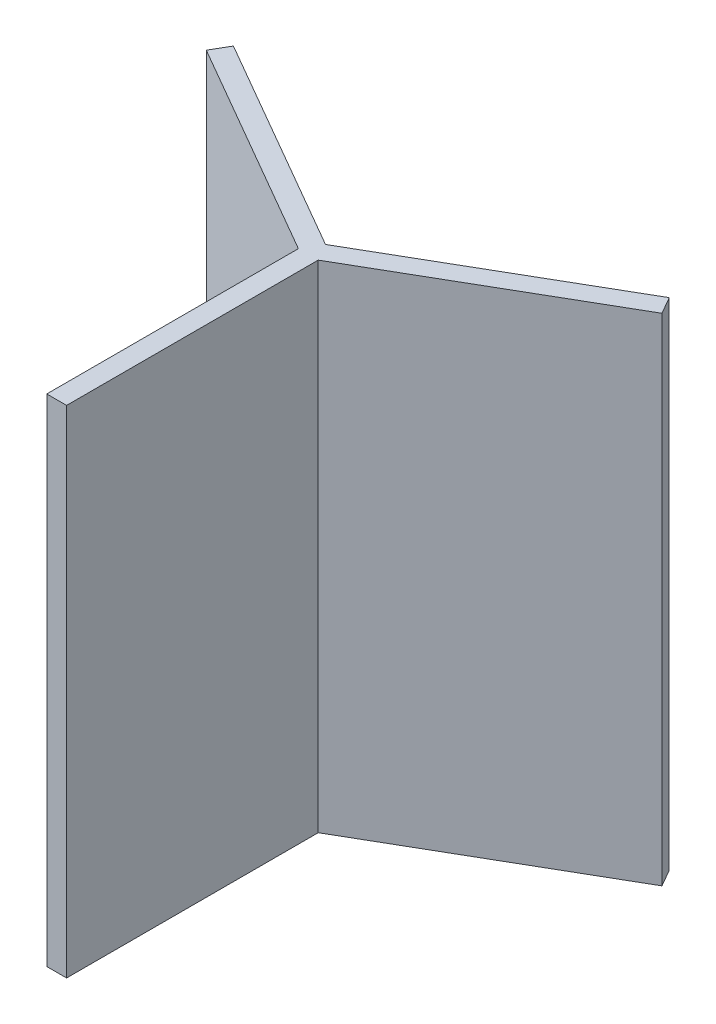
SolidWorks part; units mm, degrees
ref_plane "Front Plane" through (0, 0, 0) normal (0, 0, 1) x (1, 0, 0)
ref_plane "Top Plane" through (0, 0, 0) normal (0, 1, 0) x (1, 0, 0)
ref_plane "Right Plane" through (0, 0, 0) normal (1, 0, 0) x (0, 0, -1)
sketch "Sketch1" plane through (0, 0, 0) normal (0, 1, 0) x (1, 0, 0)
  line L0 (0, 0) -> (-2247.23, 1297.4389) construction
  line L1 (-100, -2594.8777) -> (100, -2594.8777)
  line L4 (0, 0) -> (0, -2594.8777) construction
  line L5 (-100, -2594.8777) -> (-100, -57.735)
  line L6 (0, 0) -> (100, 0) construction
  line L7 (100, -2594.8777) -> (100, -57.735)
  line L8 (-100, -2594.8777) -> (100, 0) construction
  line L9 (-100, 0) -> (100, -2594.8777) construction
  line L10 (-2297.23, 1210.8363) -> (-100, -57.735)
  line L11 (-2197.23, 1384.0414) -> (0, 115.4701)
  line L12 (-2197.23, 1384.0414) -> (-2297.23, 1210.8363)
  line L13 (50, 86.6025) -> (0, 0) construction
  line L14 (0, 0) -> (2247.23, 1297.4389) construction
  line L15 (2197.23, 1384.0414) -> (0, 115.4701)
  line L16 (2297.23, 1210.8363) -> (100, -57.735)
  line L17 (2297.23, 1210.8363) -> (2197.23, 1384.0414)
  line L18 (50, -86.6025) -> (0, 0) construction
  line L19 (0, 0) -> (-50, -86.6025) construction
  line L20 (-95.3428, -60.4238) -> (-50, -86.6025) construction
  line L21 (-100, 0) -> (0, 0) construction
  line L22 (0, 0) -> (-50, 86.6025) construction
  line L23 (100, -57.735) -> (100, 0) construction
  line L24 (-100, -57.735) -> (-100, 0) construction
  line L25 (0, 115.4701) -> (-50, 86.6025) construction
  line L26 (0, 115.4701) -> (50, 86.6025) construction
  line L27 (95.3428, -60.4238) -> (50, -86.6025) construction
  line L28 (100, -57.735) -> (95.3428, -60.4238) construction
  line L29 (-100, -57.735) -> (-95.3428, -60.4238) construction
  arc A0 (0, -2594.8777) -> (2124.6635, 1489.6964) centre (0, 0) ccw construction
  arc A1 (2124.6635, 1489.6964) -> (-2046.724, 1595.0897) centre (0, 0) ccw construction
  arc A2 (-2046.724, 1595.0897) -> (0, -2594.8777) centre (0, 0) ccw construction
  point P1 (-1023.362, 797.5449)
  point P3 (1062.3318, 744.8482)
  point P4 (0, -1297.4389)
  point P5 (0, -1297.4389)
  point P8 (0, 0)
  dimension "D1" = 200
  dimension "D2" = 3
extrude "Boss-Extrude1" add sketch "Sketch1" along normal blind 5000 contours L1 L7 L6 L4 | L6 L5 L1 L4
